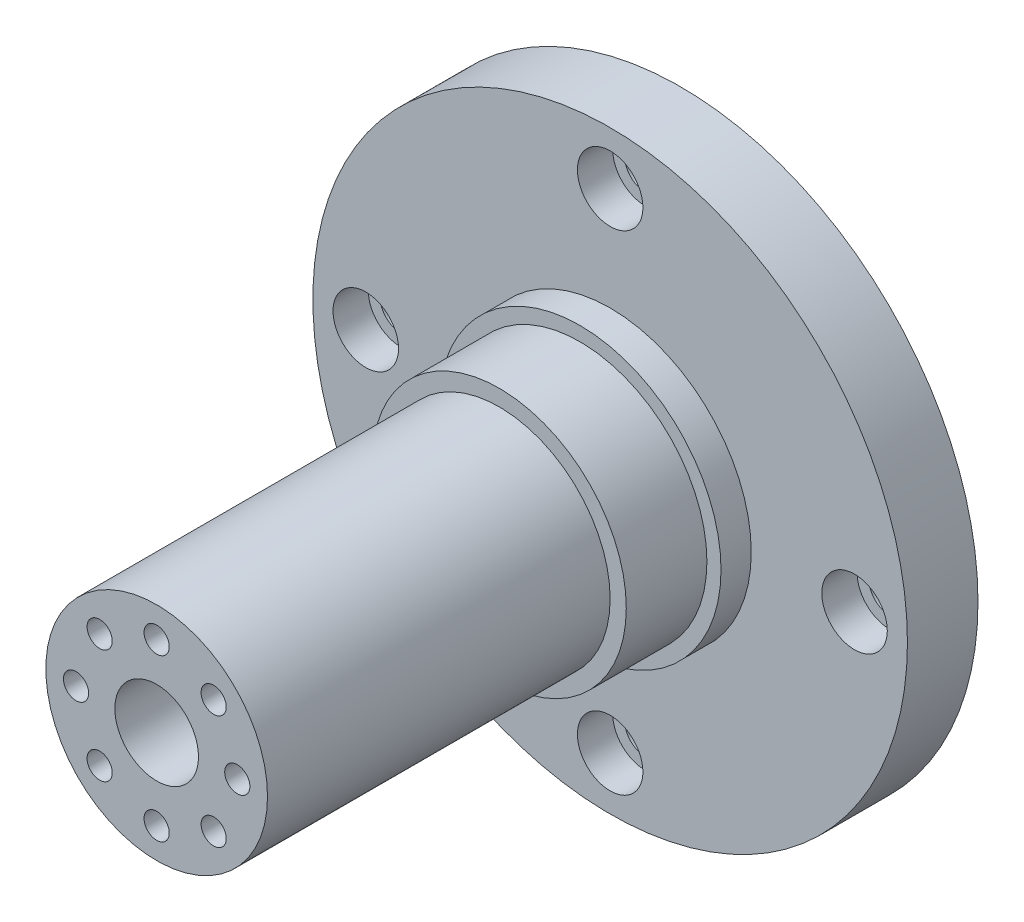
SolidWorks part; units mm, degrees
ref_plane "Front Plane" through (0, 0, 0) normal (0, 0, 1) x (1, 0, 0)
ref_plane "Top Plane" through (0, 0, 0) normal (0, 1, 0) x (1, 0, 0)
ref_plane "Right Plane" through (0, 0, 0) normal (1, 0, 0) x (0, 0, -1)
sketch "Sketch2" plane through (0, 0, 0) normal (0, 0, 1) x (1, 0, 0)
  circle A0 centre (0, 0) radius 29.5
  dimension "D1" = 59
extrude "Boss-Extrude1" add sketch "Sketch2" along normal blind 7
sketch "Sketch3" plane through (0, 0, 7) normal (0, 0, 1) x (1, 0, 0)
  circle A0 centre (0, 0) radius 14
  dimension "D1" = 28
extrude "Boss-Extrude2" add sketch "Sketch3" along normal blind 3
sketch "Sketch5" plane through (0, 0, 10) normal (0, 0, 1) x (1, 0, 0)
  circle A0 centre (0, 0) radius 12.6
  dimension "D1" = 25.2
extrude "Boss-Extrude3" add sketch "Sketch5" along normal blind 8
sketch "Sketch6" plane through (0, 0, 18) normal (0, 0, 1) x (1, 0, 0)
  circle A0 centre (0, 0) radius 11
  dimension "D1" = 22
extrude "Boss-Extrude4" add sketch "Sketch6" along normal blind 34
sketch "Sketch7" plane through (0, 0, 0) normal (0, 0, -1) x (-1, 0, 0)
  circle A0 centre (0, 0) radius 2.8234
  circle A1 centre (8, 0) radius 2.1
  circle A2 centre (5.6569, -5.6569) radius 2.1
  circle A3 centre (0, -8) radius 2.1
  circle A4 centre (-5.6569, -5.6569) radius 2.1
  circle A5 centre (-8, 0) radius 2.1
  circle A6 centre (-5.6569, 5.6569) radius 2.1
  circle A7 centre (0, 8) radius 2.1
  circle A8 centre (5.6569, 5.6569) radius 2.1
  point P22 (0, 0)
  dimension "D1" = 4.2
  dimension "D2" = 8
  dimension "D3" = 8
extrude "Cut-Extrude1" cut sketch "Sketch7" against normal blind 33.8 contours A4 | A5 | A6 | A7 | A8 | A1 | A2 | A3
sketch "Sketch8" plane through (0, 0, 33.8) normal (0, 0, -1) x (-1, 0, 0)
  circle A0 centre (-8, 0) radius 1.25
  circle A1 centre (-5.6569, 5.6569) radius 1.25
  circle A2 centre (0, 8) radius 1.25
  circle A3 centre (5.6569, 5.6569) radius 1.25
  circle A4 centre (8, 0) radius 1.25
  circle A5 centre (5.6569, -5.6569) radius 1.25
  circle A6 centre (0, -8) radius 1.25
  circle A7 centre (-5.6569, -5.6569) radius 1.25
  point P20 (0, 0)
  dimension "D1" = 2.5
  dimension "D2" = 8
extrude "Cut-Extrude2" cut sketch "Sketch8" against normal through all
sketch "Sketch9" plane through (0, 0, 52) normal (0, 0, 1) x (1, 0, 0)
  circle A0 centre (0, 0) radius 4.15
  dimension "D1" = 8.3
extrude "Cut-Extrude3" cut sketch "Sketch9" against normal blind 9
sketch "Sketch10" plane through (0, 0, 7) normal (0, 0, 1) x (1, 0, 0)
  circle A0 centre (-24.25, 0) radius 3.25
  circle A1 centre (0, 0) radius 14 construction
  circle A5 centre (0, 24.25) radius 3.25
  circle A6 centre (24.25, 0) radius 3.25
  circle A7 centre (0, -24.25) radius 3.25
  point P13 (0, 0)
  point P14 (-2.5, -2.5)
  dimension "D1" = 6.5
  dimension "D2" = 24.25
  dimension "D3" = 4
extrude "Cut-Extrude4" cut sketch "Sketch10" against normal blind 3.5
sketch "Sketch11" plane through (0, 0, 3.5) normal (0, 0, 1) x (1, 0, 0)
  circle A4 centre (0, 24.25) radius 2.07
  circle A5 centre (24.25, 0) radius 2.07
  circle A6 centre (0, -24.25) radius 2.07
  circle A7 centre (-24.25, 0) radius 2.07
  point P12 (0, 0)
  point P14 (0, 0)
  dimension "D1" = 4
  dimension "D3" = 4.14
extrude "Cut-Extrude5" cut sketch "Sketch11" against normal through all
